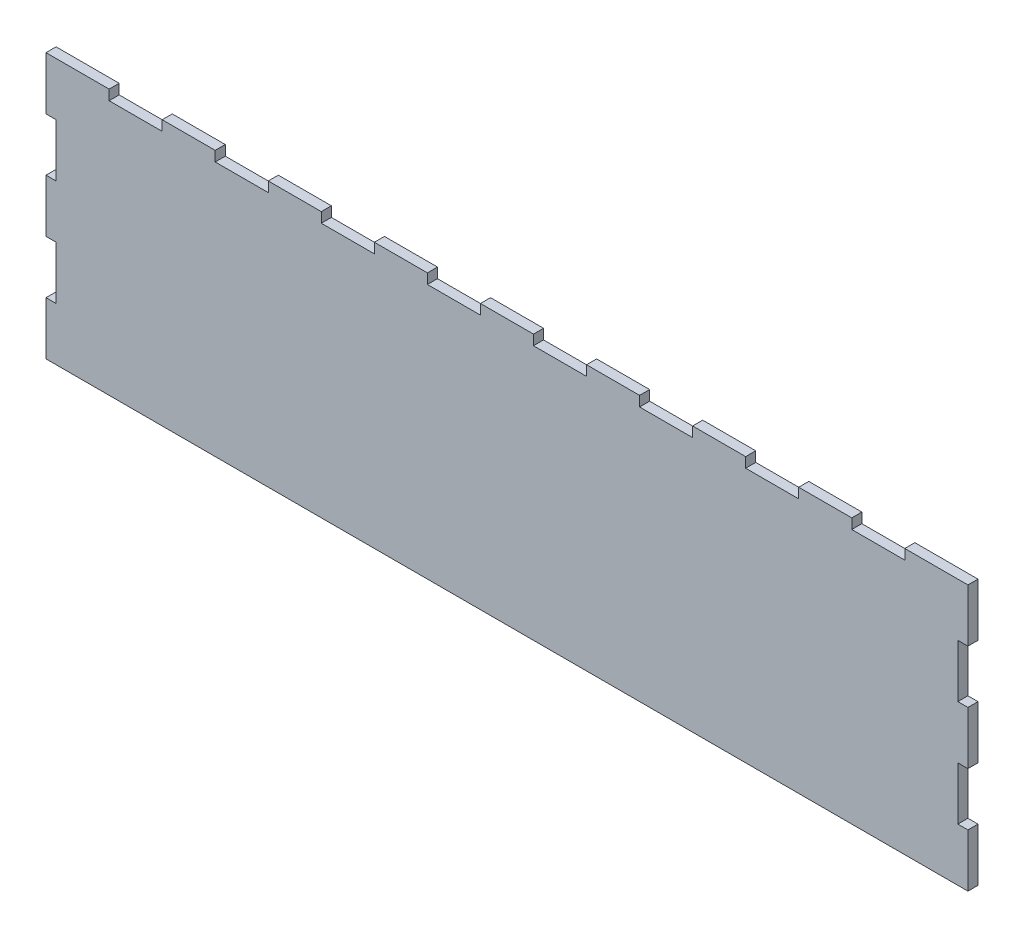
SolidWorks part; units mm, degrees
material "1060 Alloy"
ref_plane "Front Plane" through (0, 0, 0) normal (0, 0, 1) x (1, 0, 0)
ref_plane "Top Plane" through (0, 0, 0) normal (0, 1, 0) x (1, 0, 0)
ref_plane "Right Plane" through (0, 0, 0) normal (1, 0, 0) x (0, 0, -1)
sketch "Sketch1" plane through (0, 0, 0) normal (0, 0, 1) x (1, 0, 0)
  line L0 (95.25, 50.8) -> (95.25, 25.4)
  line L1 (0, 0) -> (622.3, 0) construction
  line L2 (0, 0) -> (0, 127) construction
  line L3 (0, 127) -> (622.3, 127) construction
  line L4 (622.3, 0) -> (622.3, 127) construction
  line L5 (90.424, 127) -> (531.876, 127)
  line L6 (95.25, 101.6) -> (95.25, 76.2)
  line L7 (95.25, 0) -> (527.05, 0)
  line L8 (527.05, 101.6) -> (527.05, 76.2)
  line L10 (90.424, 127) -> (90.424, 101.6)
  line L11 (90.424, 101.6) -> (95.25, 101.6)
  line L12 (527.05, 50.8) -> (527.05, 25.4)
  line L13 (95.25, 76.2) -> (90.424, 76.2)
  line L15 (95.25, 50.8) -> (90.424, 50.8)
  line L16 (90.424, 76.2) -> (90.424, 50.8)
  line L17 (90.424, 25.4) -> (95.25, 25.4)
  line L18 (90.424, 25.4) -> (90.424, 0)
  line L19 (90.424, 0) -> (95.25, 0)
  line L21 (527.05, 101.6) -> (531.876, 101.6)
  line L22 (531.876, 127) -> (531.876, 101.6)
  line L23 (527.05, 76.2) -> (531.876, 76.2)
  line L25 (527.05, 50.8) -> (531.876, 50.8)
  line L26 (531.876, 76.2) -> (531.876, 50.8)
  line L27 (527.05, 25.4) -> (531.876, 25.4)
  line L29 (527.05, 0) -> (531.876, 0)
  line L30 (531.876, 25.4) -> (531.876, 0)
  dimension "D1" = 127
  dimension "D2" = 622.3
  dimension "D3" = 95.25
  dimension "D4" = 95.25
  dimension "D5" = 4.826
extrude "Boss-Extrude1" add sketch "Sketch1" along normal blind 4.826
sketch "Sketch2" plane through (0, 127, 0) normal (0, 1, 0) x (1, 0, 0)
  line L0 (531.876, 0) -> (90.424, 0) construction
  line L1 (120.65, 0) -> (146.05, 0)
  line L2 (120.65, 0) -> (120.65, -4.826)
  line L3 (120.65, -4.826) -> (146.05, -4.826)
  line L4 (146.05, 0) -> (146.05, -4.826)
  line L5 (531.876, -4.826) -> (90.424, -4.826) construction
  line L6 (90.424, -4.826) -> (90.424, 0) construction
  line L7 (95.25, 14.224) -> (95.25, 0) construction
  line L8 (171.45, -4.826) -> (196.85, -4.826)
  line L9 (196.85, 0) -> (196.85, -4.826)
  line L10 (171.45, 0) -> (196.85, 0)
  line L11 (171.45, 0) -> (171.45, -4.826)
  line L12 (222.25, -4.826) -> (247.65, -4.826)
  line L13 (247.65, 0) -> (247.65, -4.826)
  line L14 (222.25, 0) -> (247.65, 0)
  line L15 (222.25, 0) -> (222.25, -4.826)
  line L16 (273.05, -4.826) -> (298.45, -4.826)
  line L17 (298.45, 0) -> (298.45, -4.826)
  line L18 (273.05, 0) -> (298.45, 0)
  line L19 (273.05, 0) -> (273.05, -4.826)
  line L20 (323.85, -4.826) -> (349.25, -4.826)
  line L21 (349.25, 0) -> (349.25, -4.826)
  line L22 (323.85, 0) -> (349.25, 0)
  line L23 (323.85, 0) -> (323.85, -4.826)
  line L24 (374.65, -4.826) -> (400.05, -4.826)
  line L25 (400.05, 0) -> (400.05, -4.826)
  line L26 (374.65, 0) -> (400.05, 0)
  line L27 (374.65, 0) -> (374.65, -4.826)
  line L28 (425.45, -4.826) -> (450.85, -4.826)
  line L29 (450.85, 0) -> (450.85, -4.826)
  line L30 (425.45, 0) -> (450.85, 0)
  line L31 (425.45, 0) -> (425.45, -4.826)
  line L32 (476.25, -4.826) -> (501.65, -4.826)
  line L33 (501.65, 0) -> (501.65, -4.826)
  line L34 (476.25, 0) -> (501.65, 0)
  line L35 (476.25, 0) -> (476.25, -4.826)
  point P8 (90.424, -2.413)
  dimension "D1" = 25.4
  dimension "D2" = 25.4
  dimension "D3" = 8
extrude "Cut-Extrude1" cut sketch "Sketch2" against normal blind 4.826
equation "\"sheet width\"= .19"
equation "\"width\"= 24.5"
equation "\"length\"= 34.5"
equation "\"standoff hole size\"= .5"
equation "\"ground clearence\"= 3"
equation "\"small drive pulley\"= 74.55mm"
equation "\"large drive pulley\"= 150.95mm"
equation "\"drive axle hole size\"= .5"
equation "\"front pulley clearence\"= 1"
equation "\"center support location\"= 19"
equation "\"inner to outer wall size\"= 3.75"
equation "\"D2@Sketch1\"=\"width\""
equation "\"D3@Sketch1\"=\"inner to outer wall size\""
equation "\"D4@Sketch1\"=\"inner to outer wall size\""
equation "\"D5@Sketch1\"=\"sheet width\""
equation "\"D1@Boss-Extrude1\"=\"sheet width\""
equation "\"D1@Cut-Extrude1\"=\"sheet width\""
